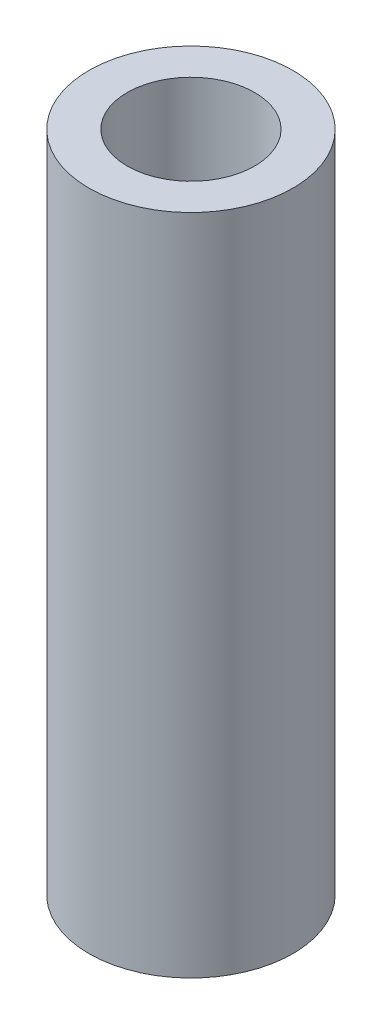
SolidWorks part; units mm, degrees
material "1060 Alloy"
ref_plane "Front Plane" through (0, 0, 0) normal (0, 0, 1) x (1, 0, 0)
ref_plane "Top Plane" through (0, 0, 0) normal (0, 1, 0) x (1, 0, 0)
ref_plane "Right Plane" through (0, 0, 0) normal (1, 0, 0) x (0, 0, -1)
sketch "Sketch1" plane through (0, 0, 0) normal (0, 1, 0) x (1, 0, 0)
  circle A0 centre (0, 0) radius 4
  circle A1 centre (0, 0) radius 2.5
  dimension "D1" = 8
  dimension "D2" = 5
extrude "Boss-Extrude1" add sketch "Sketch1" along normal blind 26
